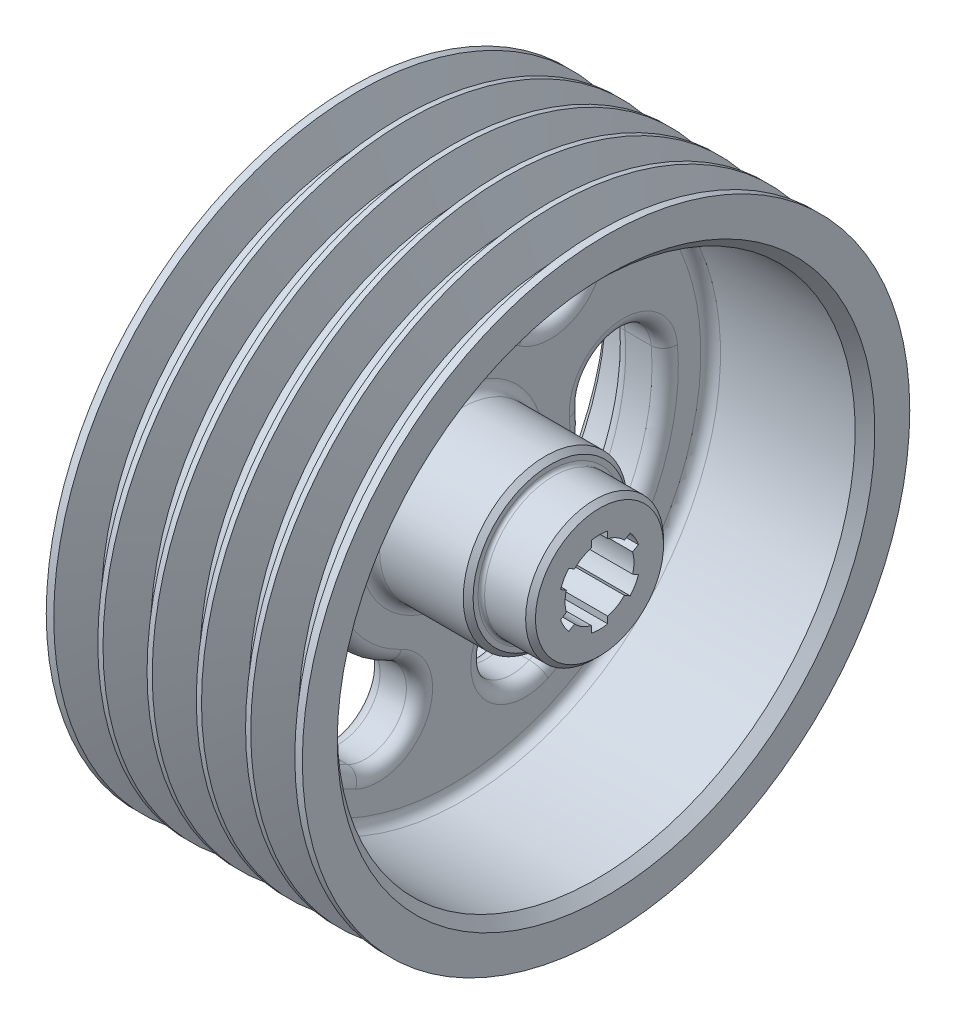
SolidWorks part; units mm, degrees
ref_plane "Front Plane" through (0, 0, 0) normal (0, 0, 1) x (1, 0, 0)
ref_plane "Top Plane" through (0, 0, 0) normal (0, 1, 0) x (1, 0, 0)
ref_plane "Right Plane" through (0, 0, 0) normal (1, 0, 0) x (0, 0, -1)
sketch "Sketch1" plane through (0, 0, 0) normal (0, 0, 1) x (1, 0, 0)
  line L0 (-41.1529, 0) -> (128.89, 0) construction
  line L1 (76, 0) -> (25, 0)
  line L2 (25, 0) -> (25, 12)
  line L3 (24, 13) -> (15, 13)
  line L4 (15, 13) -> (15, 72)
  line L5 (12, 75) -> (3, 75)
  line L6 (0, 78) -> (0, 92.5)
  line L7 (0, 92.5) -> (2.2916, 92.5)
  line L8 (78, 92.5) -> (78, 81.8657)
  line L9 (75, 78.8657) -> (34, 78.8657)
  line L10 (31, 75.8657) -> (31, 28)
  line L11 (34, 25) -> (59.5, 25)
  line L12 (61, 23.5) -> (61, 22)
  line L13 (62, 21) -> (74.5, 21)
  line L14 (76, 19.5) -> (76, 0)
  line L15 (3, 75) -> (0, 78)
  line L16 (78, 81.8657) -> (75, 78.8657)
  line L17 (74.5, 21) -> (76, 19.5)
  line L18 (59.5, 25) -> (61, 23.5)
  line L19 (75.7084, 92.5) -> (72, 81.73)
  line L20 (72, 81.73) -> (66, 81.73)
  line L21 (66, 81.73) -> (62.2916, 92.5)
  line L22 (69, 85.719) -> (69, 96.9051) construction
  line L23 (75.7084, 92.5) -> (78, 92.5)
  line L24 (51, 81.73) -> (47.2916, 92.5)
  line L25 (57, 81.73) -> (51, 81.73)
  line L26 (60.7084, 92.5) -> (57, 81.73)
  line L27 (36, 81.73) -> (32.2916, 92.5)
  line L28 (42, 81.73) -> (36, 81.73)
  line L29 (45.7084, 92.5) -> (42, 81.73)
  line L30 (21, 81.73) -> (17.2916, 92.5)
  line L31 (27, 81.73) -> (21, 81.73)
  line L32 (30.7084, 92.5) -> (27, 81.73)
  line L33 (6, 81.73) -> (2.2916, 92.5)
  line L34 (12, 81.73) -> (6, 81.73)
  line L35 (15.7084, 92.5) -> (12, 81.73)
  line L36 (15.7084, 92.5) -> (17.2916, 92.5)
  line L37 (30.7084, 92.5) -> (32.2916, 92.5)
  line L38 (45.7084, 92.5) -> (47.2916, 92.5)
  line L39 (60.7084, 92.5) -> (62.2916, 92.5)
  arc A0 (31, 28) -> (34, 25) centre (34, 28) ccw
  arc A1 (34, 78.8657) -> (31, 75.8657) centre (34, 75.8657) ccw
  arc A2 (15, 72) -> (12, 75) centre (12, 72) ccw
  arc A3 (25, 12) -> (24, 13) centre (24, 12) ccw
  arc A4 (61, 22) -> (62, 21) centre (62, 22) ccw
  point P9 (0, 75)
  point P11 (78, 78.8657)
  point P15 (61, 25)
  point P17 (76, 21)
  point P29 (31, 78.8657)
  point P32 (15, 75)
  point P35 (25, 13)
  point P38 (61, 21)
  dimension "D12" = 3
  dimension "D13" = 1
  dimension "D1" = 92.5
  dimension "D2" = 75
  dimension "D3" = 15
  dimension "D4" = 10
  dimension "D5" = 13
  dimension "D6" = 78
  dimension "D7" = 2
  dimension "D8" = 47
  dimension "D9" = 15
  dimension "D10" = 21
  dimension "D11" = 25
  dimension "D18" = 38
  dimension "D19" = 10.77
  dimension "D20" = 9
  dimension "D21" = 6
  dimension "D22" = 5
revolve "Revolve1" add sketch "Sketch1" angle 360 about L0
sketch "Sketch2" plane through (76, 0, 0) normal (1, 0, 0) x (0, 0, -1)
  line L0 (0, 56.6493) -> (0, -58.7426) construction
  line L1 (-57.5651, 0) -> (41.8656, 0) construction
  line L2 (2.5, 12.2474) -> (2.5, 10.198)
  line L3 (-2.5, 12.2474) -> (-2.5, 10.198)
  line L4 (9.3566, 8.2888) -> (7.5818, 7.2641)
  line L5 (11.8566, 3.9587) -> (10.0818, 2.934)
  line L6 (11.8566, -3.9587) -> (10.0818, -2.934)
  line L7 (9.3566, -8.2888) -> (7.5818, -7.2641)
  line L8 (2.5, -12.2474) -> (2.5, -10.198)
  line L9 (-2.5, -12.2474) -> (-2.5, -10.198)
  line L10 (-9.3566, -8.2888) -> (-7.5818, -7.2641)
  line L11 (-11.8566, -3.9587) -> (-10.0818, -2.934)
  line L12 (-11.8566, 3.9587) -> (-10.0818, 2.934)
  line L13 (-9.3566, 8.2888) -> (-7.5818, 7.2641)
  arc A0 (-2.5, 10.198) -> (-7.5818, 7.2641) centre (0, 0) ccw
  arc A2 (2.5, 12.2474) -> (-2.5, 12.2474) centre (0, 0) ccw
  arc A3 (11.8566, 3.9587) -> (9.3566, 8.2888) centre (0, 0) ccw
  arc A4 (9.3566, -8.2888) -> (11.8566, -3.9587) centre (0, 0) ccw
  arc A5 (-2.5, -12.2474) -> (2.5, -12.2474) centre (0, 0) ccw
  arc A6 (-11.8566, -3.9587) -> (-9.3566, -8.2888) centre (0, 0) ccw
  arc A7 (-9.3566, 8.2888) -> (-11.8566, 3.9587) centre (0, 0) ccw
  arc A8 (-10.0818, 2.934) -> (-10.0818, -2.934) centre (0, 0) ccw
  arc A9 (7.5818, 7.2641) -> (2.5, 10.198) centre (0, 0) ccw
  arc A10 (10.0818, -2.934) -> (10.0818, 2.934) centre (0, 0) ccw
  arc A11 (-7.5818, -7.2641) -> (-2.5, -10.198) centre (0, 0) ccw
  arc A12 (2.5, -10.198) -> (7.5818, -7.2641) centre (0, 0) ccw
  point P32 (0, 0)
  dimension "D1" = 6
  dimension "D2" = 21
  dimension "D3" = 5
extrude "Cut-Extrude1" cut sketch "Sketch2" against normal through all
sketch "Sketch3" plane through (31, 0, 0) normal (1, 0, 0) x (0, 0, -1)
  line L0 (0, 0) -> (0, 75.8657) construction
  circle A0 centre (0, 0) radius 75.8657 construction
  arc A1 (-30, 43.0842) -> (30, 43.0842) centre (0, 0) cw construction
  arc A2 (37.1429, 53.3424) -> (-37.1429, 53.3424) centre (0, 0) ccw
  arc A3 (22.8571, 32.8261) -> (-22.8571, 32.8261) centre (0, 0) ccw
  arc A4 (22.8571, 32.8261) -> (37.1429, 53.3424) centre (30, 43.0842) ccw
  arc A5 (-37.1429, 53.3424) -> (-22.8571, 32.8261) centre (-30, 43.0842) ccw
  point P8 (0, 52.5)
  point P13 (0, 0)
  dimension "D1" = 65
  dimension "D2" = 25
  dimension "D3" = 60
extrude "Cut-Extrude2" cut sketch "Sketch3" against normal through all
pattern_circular "CirPattern1" count 3 over 360 about axis through (0, 0, 0) along (1, 0, 0) of "Cut-Extrude2"
fillet "Fillet1" radius 4 24 edges at (15, -52.8353, 10.9971) (15, -32.5, 56.2917) (15, 16.8939, 51.2552) (31, -52.8353, 10.9971) (31, -32.5, 56.2917) (31, 16.8939, 51.2552) (15, -52.8353, -10.9971) (15, -20, -34.641) (15, 16.8939, -51.2552) (31, -52.8353, -10.9971) (31, -20, -34.641) (31, 16.8939, -51.2552) (15, 40, 0) (15, 35.9414, 40.2581) (15, 65, 0) (31, 40, 0) (31, 35.9414, 40.2581) (31, 65, 0) (15, -20, 34.641) (31, -20, 34.641) (15, -32.5, -56.2917) (31, -32.5, -56.2917) (15, 35.9414, -40.2581) (31, 35.9414, -40.2581)
